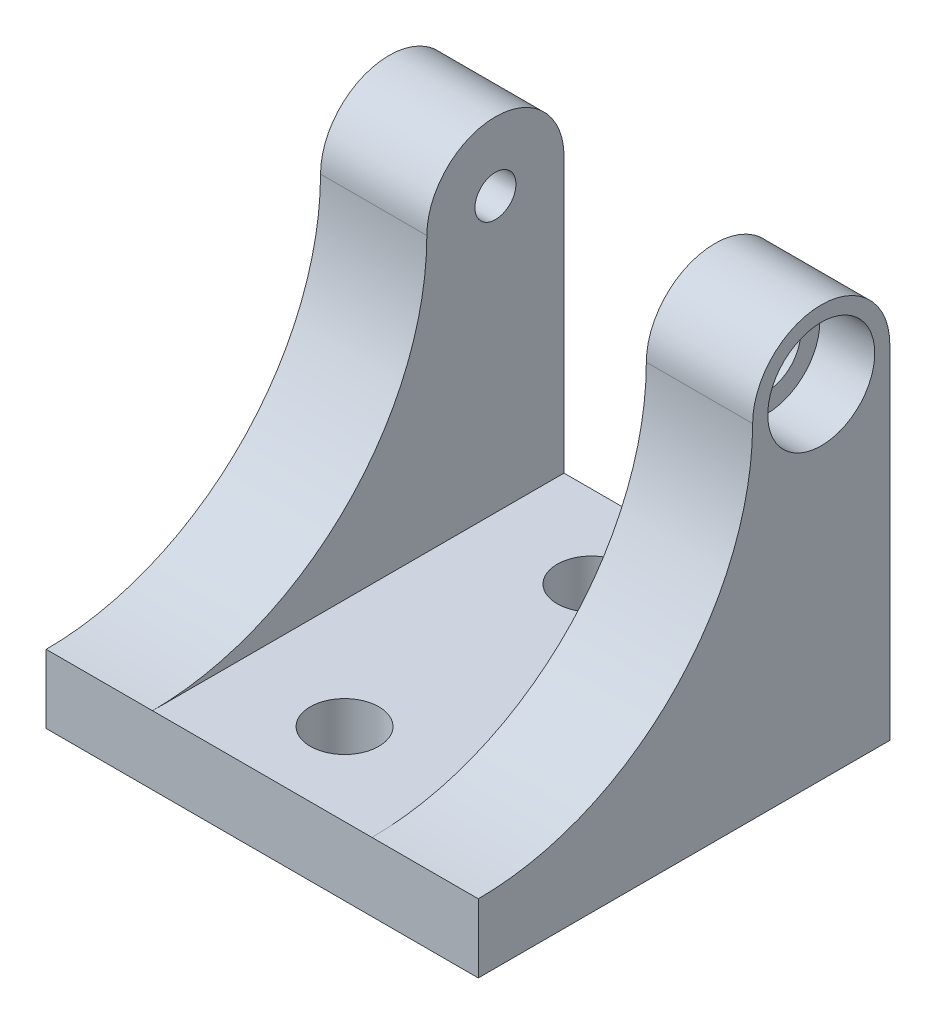
SolidWorks part; units mm, degrees
ref_plane "Front Plane" through (0, 0, 0) normal (0, 0, 1) x (1, 0, 0)
ref_plane "Top Plane" through (0, 0, 0) normal (0, 1, 0) x (1, 0, 0)
ref_plane "Right Plane" through (0, 0, 0) normal (1, 0, 0) x (0, 0, -1)
sketch "Sketch5" plane through (0, 0, 0) normal (1, 0, 0) x (0, 0, -1)
  line L0 (0, 0) -> (38.1, 0)
  line L1 (38.1, 0) -> (38.1, 31.75)
  line L2 (0, 0) -> (0, 6.35)
  line L3 (38.1, 31.75) -> (19.3097, 31.75) construction
  arc A0 (38.1, 31.75) -> (25.4, 31.75) centre (31.75, 31.75) ccw
  arc A1 (25.4, 31.75) -> (0, 6.35) centre (0, 31.75) cw
  dimension "D4" = 12.7
  dimension "D1" = 6.35
  dimension "D2" = 31.75
  dimension "D3" = 38.1
extrude "Extrude3" add sketch "Sketch5" along normal blind 40.005
sketch "Sketch6" plane through (0, 0, -38.1) normal (0, 0, -1) x (-1, 0, 0)
  line L0 (-20.0025, 0) -> (-20.0025, 48.7077) construction
  line L1 (-30.1625, 6.35) -> (-9.8425, 6.35)
  line L2 (-30.1625, 6.35) -> (-30.1625, 48.5548)
  line L3 (-30.1625, 48.5548) -> (-9.8425, 48.5548)
  line L4 (-9.8425, 6.35) -> (-9.8425, 48.5548)
  line L5 (-40.005, 0) -> (0, 0) construction
  dimension "D1" = 20.32
  dimension "D2" = 6.35
extrude "Extrude - Slot" cut sketch "Sketch6" against normal through all
sketch "Sketch8" plane through (40.005, 0, 0) normal (1, 0, 0) x (0, 0, -1)
  circle A0 centre (31.75, 31.75) radius 3.175
  arc A2 (38.1, 31.75) -> (25.4, 31.75) centre (31.75, 31.75) ccw construction
  dimension "D1" = 6.35
extrude "Extrude - shoulder through" cut sketch "Sketch8" against normal up to surface (9.8425 mm away) up to face at (30.1625, 19.3224, -26.7151)
sketch "Sketch9" plane through (40.005, 0, 0) normal (1, 0, 0) x (0, 0, -1)
  circle A0 centre (31.75, 31.75) radius 4.953
  dimension "D1" = 9.906
extrude "Extrude - cntr bore" cut sketch "Sketch9" against normal blind 5.08
sketch "Sketch10" plane through (0, 0, 0) normal (-1, 0, 0) x (0, 0, 1)
  point P0 (-31.75, 31.75)
hole_wizard "#10-24 Tapped Hole1" positions "3DSketch1" profile "Sketch11" tap size "#10-24" standard "Ansi Inch"
sketch3d "3DSketch1"
  point P0 (0, 31.75, -31.75)
sketch "Sketch11" plane through (0, 31.75, -31.75) normal (0, 1, 0) x (0, 0, 1)
  line L0 (0, 0) -> (0, 13.9678)
  line L1 (0, 13.9678) -> (1.8986, 12.827)
  line L2 (1.8986, 12.827) -> (1.8986, 0)
  line L5 (1.8986, 0) -> (0, 0)
  line L10 (0, 13.9678) -> (-1.8987, 12.827) construction
  line L11 (0, -6.35) -> (0, 107.95) construction
  dimension "Tap Drill Dia." = 3.7973
  dimension "Tap Drill Depth" = 12.827
  dimension "Drill Angle" = 118
cosmetic thread "Hole Thread1" parameters "D1"=5.715, "D2"=4.826
sketch "Sketch13" plane through (0, 0, 0) normal (0, -1, 0) x (1, 0, 0)
  line L0 (20.0025, -38.1) -> (20.0025, 0) construction
  line L1 (40.005, -38.1) -> (0, -38.1) construction
  line L2 (40.005, 0) -> (0, 0) construction
  line L4 (0, 0) -> (0, -38.1) construction
  line L5 (0, -19.05) -> (40.005, -19.05) construction
  line L6 (40.005, 0) -> (40.005, -38.1) construction
  circle A0 centre (20.0025, -7.62) radius 3.175
  circle A1 centre (20.0025, -30.48) radius 3.175
  dimension "D1" = 6.35
  dimension "D2" = 22.86
extrude "Extrude7" cut sketch "Sketch13" against normal through all
